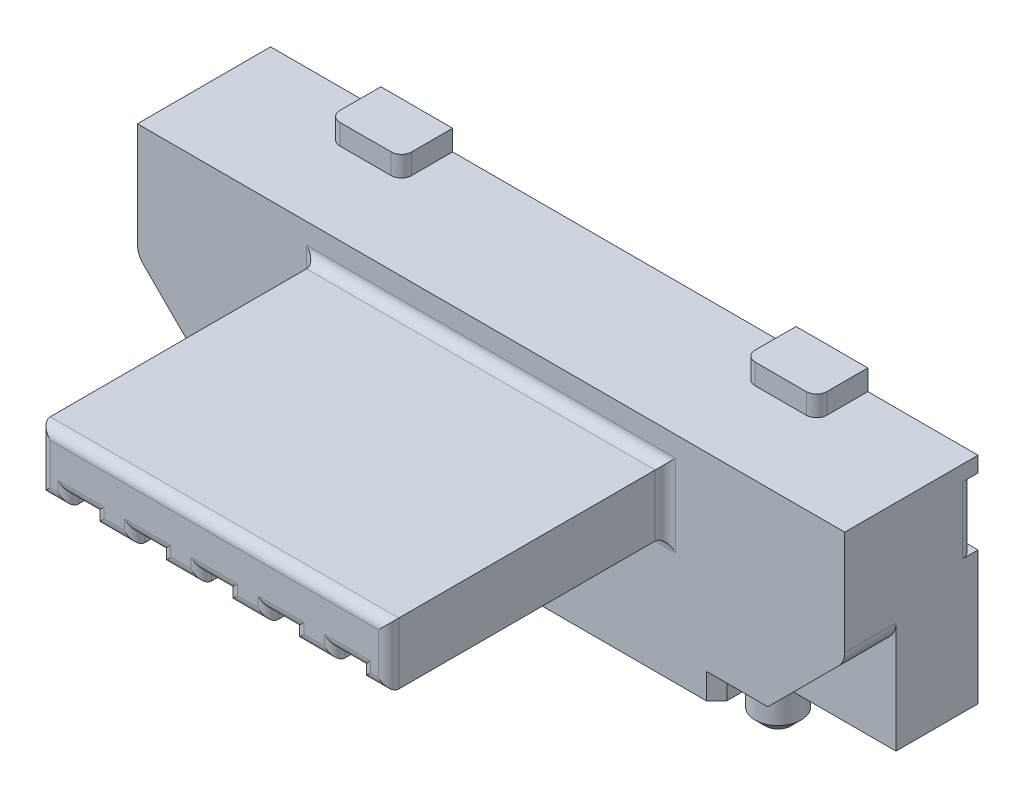
SolidWorks part; units mm, degrees
material "ABS"
ref_plane "Front Plane" through (0, 0, 0) normal (0, 0, 1) x (1, 0, 0)
ref_plane "Top Plane" through (0, 0, 0) normal (0, 1, 0) x (1, 0, 0)
ref_plane "Right Plane" through (0, 0, 0) normal (1, 0, 0) x (0, 0, -1)
sketch "Sketch1" plane through (0, 0, 0) normal (0, 1, 0) x (1, 0, 0)
  line L0 (0, -55) -> (0, 55) construction
  line L1 (-3.45, 4.8) -> (3.45, 4.8)
  line L2 (-3.45, 4.8) -> (-3.45, 3.5)
  line L3 (-3.45, 3.5) -> (3.45, 3.5)
  line L4 (3.45, 4.8) -> (3.45, 3.5)
  line L5 (-55, 0) -> (55, 0) construction
  dimension "D1" = 6.9
  dimension "D2" = 3.45
  dimension "D3" = 3.5
  dimension "D4" = 4.8
extrude "Boss-Extrude1" add sketch "Sketch1" along normal blind 2.1
sketch "Sketch2" plane through (0, 0, -3.5) normal (0, 0, 1) x (1, 0, 0)
  line L0 (0, -0.715) -> (0, 0.715) construction
  line L1 (-1.7, 1.8) -> (1.7, 1.8)
  line L2 (-1.7, 1.8) -> (-1.7, 1.2)
  line L3 (-1.7, 1.2) -> (1.7, 1.2)
  line L4 (1.7, 1.8) -> (1.7, 1.2)
  line L5 (-3.45, 2.1) -> (3.45, 2.1) construction
  dimension "D1" = 3.4
  dimension "D2" = 0.6
  dimension "D3" = 1.7
  dimension "D4" = 0.3
extrude "Boss-Extrude2" add sketch "Sketch2" along normal blind 2.7
sketch "Sketch3" plane through (0, 0, -0.8) normal (0, 0, 1) x (1, 0, 0)
  line L0 (-1.7, 1.2) -> (1.7, 1.2) construction
  line L1 (-1.425, 1.2) -> (-1.175, 1.2)
  line L2 (-1.425, 1.2) -> (-1.425, 1.3)
  line L3 (-1.425, 1.3) -> (-1.175, 1.3)
  line L4 (-1.175, 1.2) -> (-1.175, 1.3)
  line L5 (-1.7, 1.2) -> (1.7, 1.2) construction
  line L6 (-0.775, 1.2) -> (-0.525, 1.2)
  line L7 (-0.775, 1.2) -> (-0.775, 1.3)
  line L8 (-0.775, 1.3) -> (-0.525, 1.3)
  line L9 (-0.525, 1.2) -> (-0.525, 1.3)
  line L10 (-1.175, 1.3) -> (-0.775, 1.3) construction
  line L11 (-0.125, 1.2) -> (0.125, 1.2)
  line L12 (-0.125, 1.2) -> (-0.125, 1.3)
  line L13 (-0.125, 1.3) -> (0.125, 1.3)
  line L14 (0.125, 1.2) -> (0.125, 1.3)
  line L15 (0.525, 1.2) -> (0.775, 1.2)
  line L16 (0.525, 1.2) -> (0.525, 1.3)
  line L17 (0.525, 1.3) -> (0.775, 1.3)
  line L18 (0.775, 1.2) -> (0.775, 1.3)
  line L19 (1.175, 1.2) -> (1.425, 1.2)
  line L20 (1.175, 1.2) -> (1.175, 1.3)
  line L21 (1.175, 1.3) -> (1.425, 1.3)
  line L22 (1.425, 1.2) -> (1.425, 1.3)
  line L23 (-0.525, 1.3) -> (-0.125, 1.3) construction
  line L24 (0.125, 1.3) -> (0.525, 1.3) construction
  line L25 (0.775, 1.3) -> (1.175, 1.3) construction
  line L26 (0, -1.155) -> (0, 1.155) construction
  dimension "D1" = 0.65
  dimension "D2" = 0.25
  dimension "D3" = 0.125
  dimension "D4" = 0.1
extrude "Cut-Extrude1" cut sketch "Sketch3" against normal blind 3
fillet "Fillet1" radius 0.1 33 edges at (0, 1.8, -0.8) (1.7, 1.5, -0.8) (1.5625, 1.2, -0.8) (-1.5625, 1.2, -0.8) (-1.7, 1.5, -0.8) (-1.7, 1.5, -3.5) (0, 1.8, -3.5) (1.7, 1.5, -3.5) (1.5625, 1.2, -3.5) (-1.5625, 1.2, -3.5) (0.975, 1.2, -0.8) (0.775, 1.25, -0.8) (0.65, 1.3, -0.8) (0.525, 1.25, -0.8) (0.325, 1.2, -0.8) (0.125, 1.25, -0.8) (0, 1.3, -0.8) (-0.125, 1.25, -0.8) (-0.325, 1.2, -0.8) (-0.525, 1.25, -0.8) (-0.65, 1.3, -0.8) (-0.775, 1.25, -0.8) (-0.975, 1.2, -0.8) (-1.175, 1.25, -0.8) (-1.3, 1.3, -0.8) (-1.425, 1.25, -0.8) (1.425, 1.25, -0.8) (1.3, 1.3, -0.8) (1.175, 1.25, -0.8) (0.975, 1.2, -3.5) (0.325, 1.2, -3.5) (-0.325, 1.2, -3.5) (-0.975, 1.2, -3.5)
sketch "Sketch4" plane through (0, 0, -3.5) normal (0, 0, 1) x (1, 0, 0)
  line L0 (-2.7, 0.25) -> (-3.45, 1)
  line L1 (0.715, 0) -> (-0.715, 0) construction
  line L2 (-3.45, 2.1) -> (-3.45, 0) construction
  line L3 (-3.45, 1) -> (-3.45, 0)
  line L4 (-3.45, 0) -> (-2.2, 0)
  line L5 (3.45, 1) -> (2.7, 0.25)
  line L6 (3.45, 2.1) -> (3.45, 0) construction
  line L7 (3.45, 0) -> (2.2, 0)
  line L8 (3.45, 0) -> (3.45, 1)
  line L9 (-2.7, 0.25) -> (-2.2, 0.25)
  line L10 (-2.2, 0.25) -> (-2.2, 0)
  line L11 (2.7, 0.25) -> (2.2, 0.25)
  line L12 (2.2, 0.25) -> (2.2, 0)
  line L13 (0, -1.155) -> (0, 1.155) construction
  dimension "D1" = 1
  dimension "D2" = 0.25
  dimension "D3" = 2.2
  dimension "D4" = 1
  dimension "D5" = 45
  dimension "D6" = 45
extrude "Cut-Extrude2" cut sketch "Sketch4" against normal blind 0.5
fillet "Fillet3" radius 0.2 2 edges at (3.45, 1, -3.75) (-3.45, 1, -3.75)
chamfer "Chamfer1" distance 0.1 angle 45 2 edges at (-2.2, 0.125, -3.5) (2.2, 0.125, -3.5)
sketch "Sketch5" plane through (0, 0, -4.8) normal (0, 0, -1) x (-1, 0, 0)
  line L0 (-3.45, 2.1) -> (-3.45, 0) construction
  line L1 (-3.45, 1.95) -> (-2.25, 1.95)
  line L2 (-3.45, 1.95) -> (-3.45, 1.3)
  line L3 (-3.45, 1.3) -> (-2.25, 1.3)
  line L4 (-2, 1.7) -> (-2, 1.55)
  line L5 (0.715, 0) -> (-0.715, 0) construction
  line L6 (0, 1.155) -> (0, -1.155) construction
  line L7 (3.45, 2.1) -> (3.45, 0) construction
  line L8 (3.45, 1.95) -> (2.25, 1.95)
  line L9 (3.45, 1.95) -> (3.45, 1.3)
  line L10 (3.45, 1.3) -> (2.25, 1.3)
  line L11 (2, 1.7) -> (2, 1.55)
  arc A0 (2.25, 1.95) -> (2, 1.7) centre (2.25, 1.7) ccw
  arc A1 (2, 1.55) -> (2.25, 1.3) centre (2.25, 1.55) ccw
  arc A2 (-2.25, 1.3) -> (-2, 1.55) centre (-2.25, 1.55) ccw
  arc A3 (-2.25, 1.95) -> (-2, 1.7) centre (-2.25, 1.7) cw
  point P22 (-2, 1.3)
  point P25 (-2, 1.95)
  dimension "D4" = 0.25
  dimension "D1" = 0.65
  dimension "D2" = 1.3
  dimension "D3" = 2
extrude "Cut-Extrude3" cut sketch "Sketch5" against normal blind 0.05
fillet "Fillet4" radius 0.1 2 edges at (-3.45, 1.625, -4.75) (3.45, 1.625, -4.75)
sketch "Sketch6" plane through (0, 0, 0) normal (0, -1, 0) x (1, 0, 0)
  line L0 (0, -1.155) -> (0, 1.155) construction
  line L1 (1.155, 0) -> (-1.155, 0) construction
  circle A0 centre (2, -4.3) radius 0.225
  circle A1 centre (-2, -4.3) radius 0.225
  dimension "D3" = 0.45
  dimension "D1" = 2
  dimension "D2" = 2
  dimension "D4" = 4.3
extrude "Boss-Extrude3" add sketch "Sketch6" along normal blind 0.6
chamfer "Chamfer2" distance 0.1 angle 45 2 edges at (-2, -0.6, -4.525) (2, -0.6, -4.525)
sketch "Sketch7" plane through (0, 0, 0) normal (0, -1, 0) x (1, 0, 0)
  line L1 (3.45, -4.8) -> (-3.45, -4.8) construction
  line L2 (-1.7, -4.8) -> (1.7, -4.8)
  line L3 (-1.7, -4.8) -> (-1.7, -4.1)
  line L4 (-1.7, -4.1) -> (1.7, -4.1)
  line L6 (1.7, -4.8) -> (1.7, -4.1)
  line L7 (0, -1.485) -> (0, 1.485) construction
  dimension "D1" = 3.4
  dimension "D2" = 1.7
  dimension "D3" = 0.7
extrude "Cut-Extrude4" cut sketch "Sketch7" against normal blind 0.3
sketch "Sketch8" plane through (0, 2.1, 0) normal (0, 1, 0) x (1, 0, 0)
  line L0 (3.45, 4.8) -> (-3.45, 4.8) construction
  line L1 (-2.375, 4.8) -> (-1.675, 4.8)
  line L2 (-2.375, 4.8) -> (-2.375, 4.4)
  line L3 (-2.275, 4.3) -> (-1.775, 4.3)
  line L4 (-1.675, 4.8) -> (-1.675, 4.4)
  line L5 (0, -1.485) -> (0, 1.485) construction
  line L6 (1.675, 4.8) -> (2.375, 4.8)
  line L7 (1.675, 4.8) -> (1.675, 4.4)
  line L8 (1.775, 4.3) -> (2.275, 4.3)
  line L9 (2.375, 4.8) -> (2.375, 4.4)
  arc A0 (-2.375, 4.4) -> (-2.275, 4.3) centre (-2.275, 4.4) ccw
  arc A1 (-1.775, 4.3) -> (-1.675, 4.4) centre (-1.775, 4.4) ccw
  arc A2 (1.675, 4.4) -> (1.775, 4.3) centre (1.775, 4.4) ccw
  arc A3 (2.275, 4.3) -> (2.375, 4.4) centre (2.275, 4.4) ccw
  point P20 (2.375, 4.3)
  dimension "D4" = 0.1
  dimension "D1" = 2.375
  dimension "D2" = 2.375
  dimension "D3" = 0.5
  dimension "D5" = 0.7
extrude "Boss-Extrude4" add sketch "Sketch8" along normal blind 0.2
equation "\"`0.5\"=1"
